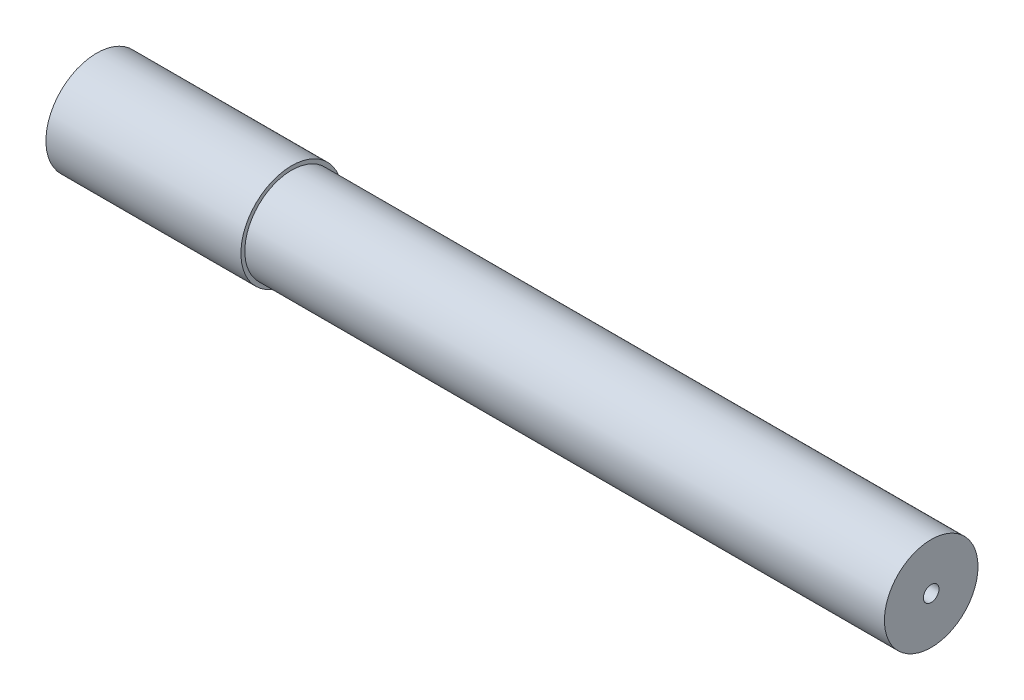
SolidWorks part; units mm, degrees
material "Tantalum"
ref_plane "Front Plane" through (0, 0, 0) normal (0, 0, 1) x (1, 0, 0)
ref_plane "Top Plane" through (0, 0, 0) normal (0, 1, 0) x (1, 0, 0)
ref_plane "Right Plane" through (0, 0, 0) normal (1, 0, 0) x (0, 0, -1)
sketch "Sketch1" plane through (0, 0, 0) normal (0, 0, 1) x (1, 0, 0)
  line L2 (11, 3.25) -> (-42.5, 3.25) construction
  line L3 (10, 0.5) -> (11, 0.5)
  line L4 (10, 0.5) -> (10, 2.25)
  line L5 (10, 2.25) -> (-42.5, 2.25)
  line L9 (-42.5, 2.25) -> (-42.5, 3.25) construction
  line L16 (-30, 3.25) -> (-42.5, 3.25)
  line L17 (-42.5, 3.25) -> (-42.5, 2.25)
  line L18 (-30, 3.25) -> (-30, 3)
  line L19 (-30, 3) -> (11, 3)
  line L20 (11, 3) -> (11, 0.5)
  dimension "D1" = 3.25
  dimension "D2" = 2.75
  dimension "D3" = 1
  dimension "D4" = 1
  dimension "D5" = 0.25
  dimension "D6" = 10
ref_axis "Axis1" through (13.5, 0, 0) along (-1, 0, 0)
revolve "Revolve1" add sketch "Sketch1" angle 360 about axis through (13.5, 0, 0) along (-1, 0, 0)
